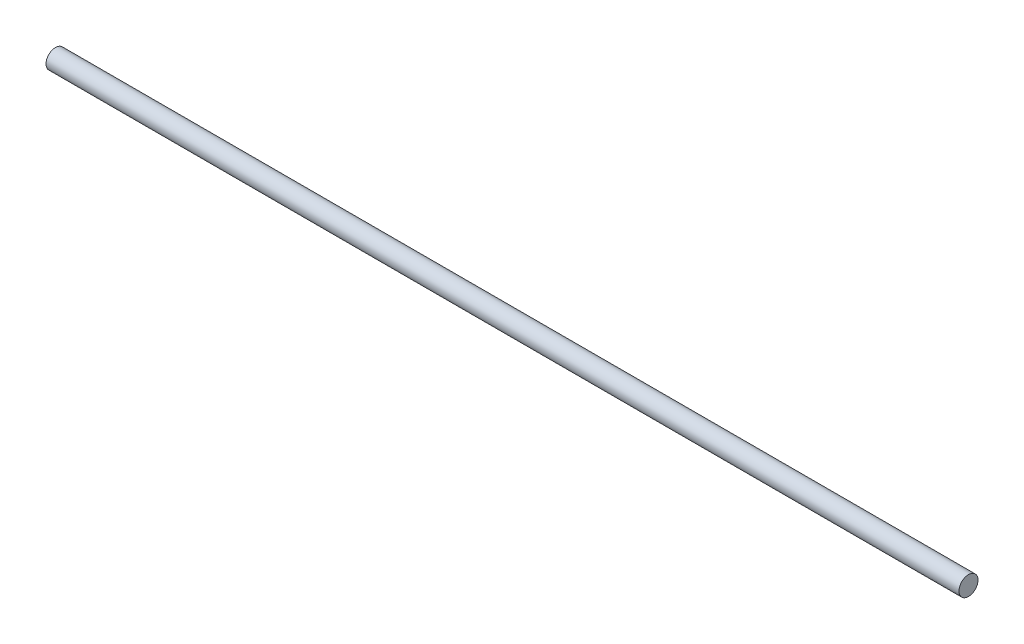
SolidWorks part; units mm, degrees
ref_plane "Front Plane" through (0, 0, 0) normal (0, 0, 1) x (1, 0, 0)
ref_plane "Top Plane" through (0, 0, 0) normal (0, 1, 0) x (1, 0, 0)
ref_plane "Right Plane" through (0, 0, 0) normal (1, 0, 0) x (0, 0, -1)
sketch "Sketch1" plane through (0, 0, 0) normal (0, 1, 0) x (1, 0, 0)
  line L0 (0, 0) -> (-914.4, 0)
  dimension "D1" = 914.4
sweep "Sweep1" add path "Sketch1" circular profile diameter 19.05 parameters "D3"=19.05
